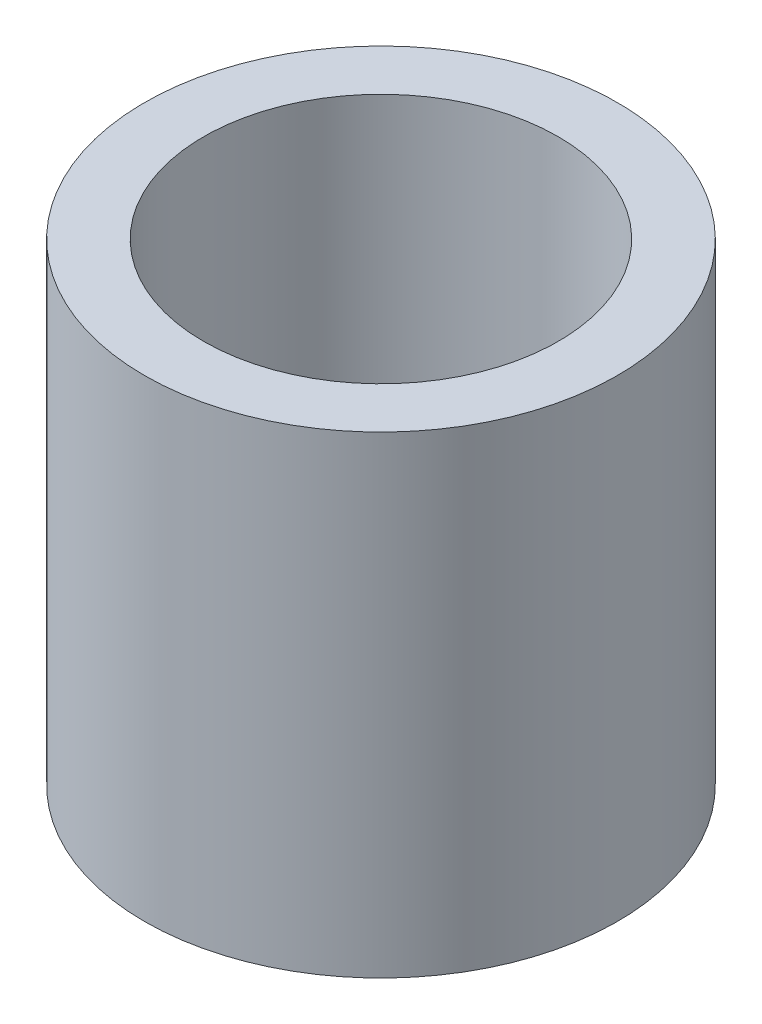
SolidWorks part; units mm, degrees
material "Brass"
ref_plane "Front Plane" through (0, 0, 0) normal (0, 0, 1) x (1, 0, 0)
ref_plane "Top Plane" through (0, 0, 0) normal (0, 1, 0) x (1, 0, 0)
ref_plane "Right Plane" through (0, 0, 0) normal (1, 0, 0) x (0, 0, -1)
sketch "Sketch1" plane through (0, 0, 0) normal (0, 1, 0) x (1, 0, 0)
  circle A0 centre (0, 0) radius 2
  circle A1 centre (0, 0) radius 1.5
  dimension "D1" = 4
  dimension "D2" = 3
extrude "Boss-Extrude1" add sketch "Sketch1" along normal blind 4
